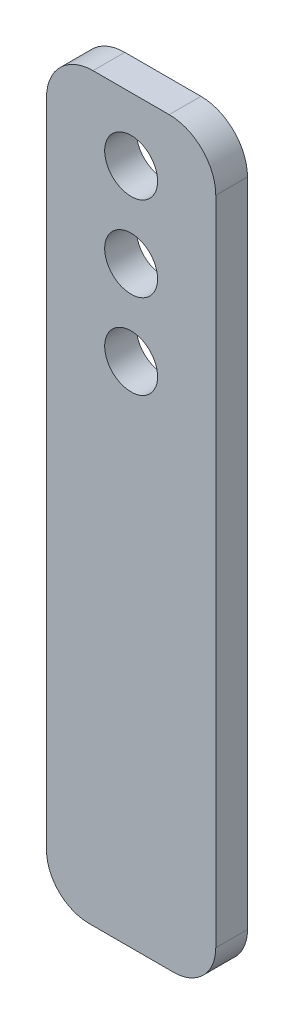
SolidWorks part; units mm, degrees
material "Acier non allié"
ref_plane "Plan de face" through (0, 0, 0) normal (0, 0, 1) x (1, 0, 0)
ref_plane "Plan de dessus" through (0, 0, 0) normal (0, 1, 0) x (1, 0, 0)
ref_plane "Plan de droite" through (0, 0, 0) normal (1, 0, 0) x (0, 0, -1)
sketch "Esquisse1" plane through (0, 0, 0) normal (0, 0, 1) x (1, 0, 0)
  line L1 (-20, -350) -> (20, -350)
  line L2 (-40, -330) -> (-40, -22)
  line L3 (-18, 0) -> (18, 0)
  line L4 (40, -330) -> (40, -22)
  circle A0 centre (0, -30) radius 12.5
  circle A1 centre (0, -70) radius 12.5
  circle A2 centre (0, -110) radius 12.5
  arc A3 (40, -22) -> (18, 0) centre (18, -22) ccw
  arc A4 (-40, -22) -> (-18, 0) centre (-18, -22) cw
  arc A5 (40, -330) -> (20, -350) centre (20, -330) cw
  arc A6 (-40, -330) -> (-20, -350) centre (-20, -330) ccw
  point P13 (40, 0)
  point P16 (-40, 0)
  point P21 (-40, -350)
  dimension "D3" = 25
  dimension "D4" = 30
  dimension "D5" = 70
  dimension "D6" = 110
  dimension "D7" = 40
  dimension "D8" = 22
  dimension "D9" = 20
  dimension "D1" = 80
  dimension "D2" = 350
extrude "Boss.-Extru.1" add sketch "Esquisse1" along normal blind 15
